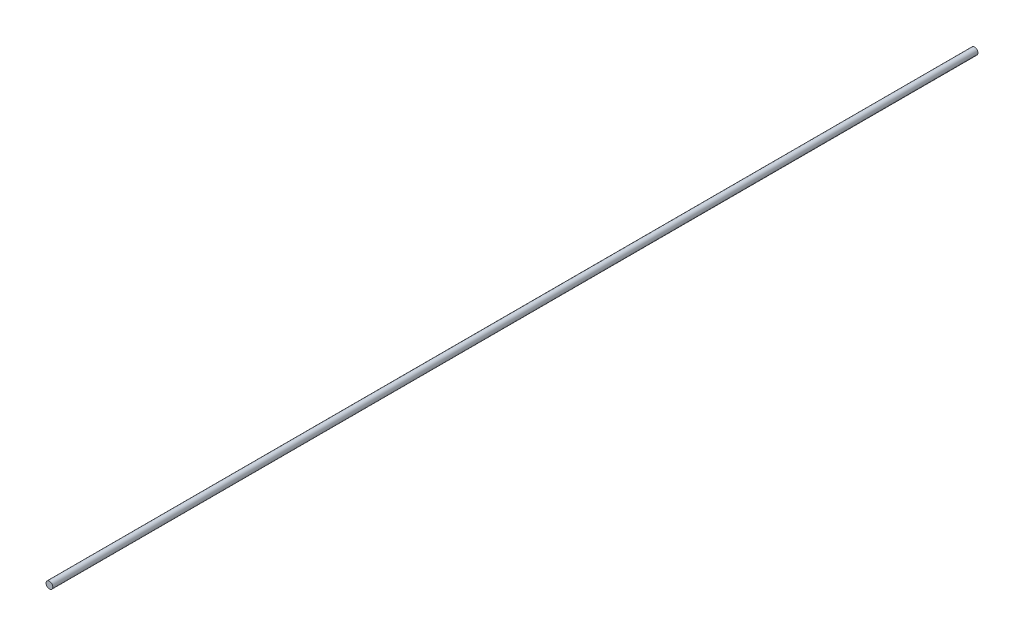
SolidWorks part; units mm, degrees
ref_plane "Front Plane" through (0, 0, 0) normal (0, 0, 1) x (1, 0, 0)
ref_plane "Top Plane" through (0, 0, 0) normal (0, 1, 0) x (1, 0, 0)
ref_plane "Right Plane" through (0, 0, 0) normal (1, 0, 0) x (0, 0, -1)
sketch "Sketch1" plane through (0, 0, 0) normal (0, 0, 1) x (1, 0, 0)
  circle A0 centre (0, 0) radius 6.35
  dimension "D1" = 12.7
extrude "Boss-Extrude1" add sketch "Sketch1" along normal mid plane 1727.2
